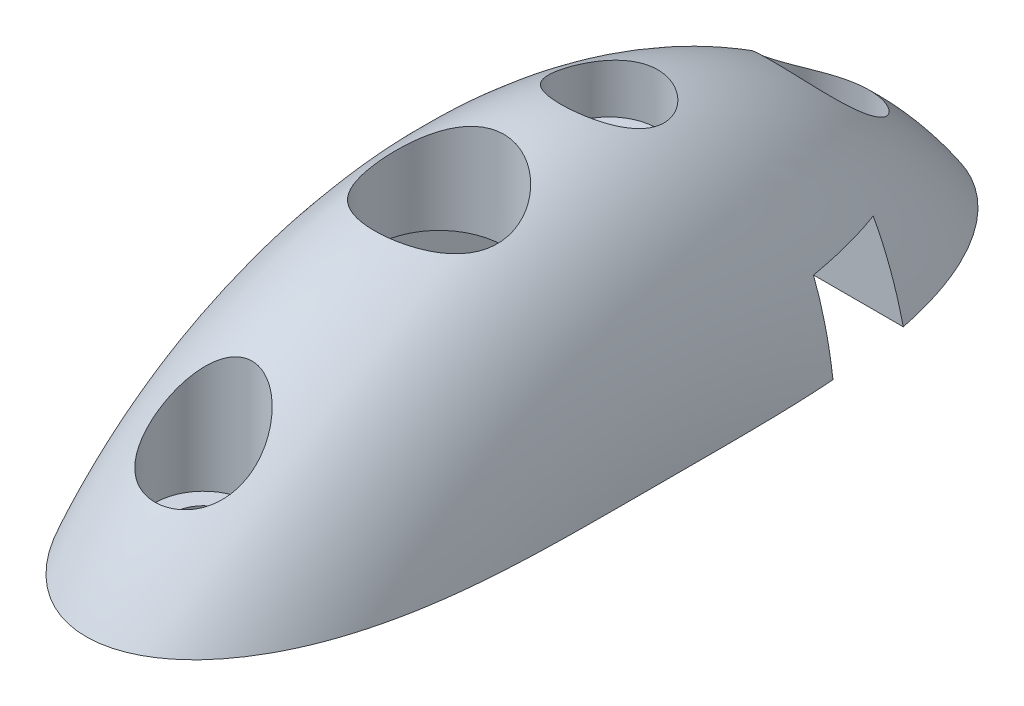
SolidWorks part; units mm, degrees
material "PET"
ref_plane "Front" through (0, 0, 0) normal (0, 0, 1) x (1, 0, 0)
ref_plane "Top" through (0, 0, 0) normal (0, 1, 0) x (1, 0, 0)
ref_plane "Right" through (0, 0, 0) normal (1, 0, 0) x (0, 0, -1)
sketch "Sketch1" plane through (0, 0, 0) normal (0, 0, 1) x (1, 0, 0)
  line L0 (0, 13.25) -> (0, 0) construction
  line L1 (-5.5, 8) -> (5.5, 8) construction
  line L2 (-5.5, 8) -> (-5.5, 0) construction
  line L3 (-5.5, 0) -> (5.5, 0) construction
  line L4 (5.5, 8) -> (5.5, 0) construction
  line L5 (-4, 8) -> (4, 8) construction
  line L6 (-4, 8) -> (-4, 13.25) construction
  line L7 (-4, 13.25) -> (4, 13.25) construction
  line L8 (4, 8) -> (4, 13.25) construction
  line L9 (-20.5845, -17.78) -> (20.5845, -17.78) construction
  line L10 (54.5, 8) -> (54.5, 13.25) construction
  line L11 (53.5, 0) -> (73.5, 0) construction
  line L12 (53.5, 0) -> (53.5, 8) construction
  line L13 (53.5, 8) -> (73.5, 8) construction
  line L14 (73.5, 0) -> (73.5, 8) construction
  line L15 (54.5, 13.25) -> (62.5, 13.25) construction
  line L16 (62.5, 13.25) -> (62.5, 8) construction
  line L17 (58.5, 13.25) -> (58.5, 0) construction
  line L18 (0, 13.97) -> (63.5, 13.97) construction
  line L19 (63.5, 13.97) -> (63.5, 0) construction
  line L20 (-9.525, 0) -> (-9.525, -17.78)
  line L21 (-9.525, -17.78) -> (9.525, -17.78)
  line L22 (9.525, -17.78) -> (9.525, 0)
  arc A1 (37.1954, 0) -> (89.8046, 0) centre (63.5, -17.78) cw construction
  ellipse E0 centre (0, 0) end of major axis (0, -13.97) minor radius 9.525 (9.525, 0) -> (-9.525, 0) ccw
  point P1 (0, 0)
  point P26 (1.8743, 17.9157)
  point P39 (0, 15.3735)
  point P40 (63.5, 14.7574)
  point P41 (34.4687, 0)
  dimension "D2" = 19.05
  dimension "D6" = 13.97
  dimension "D9" = 63.5
  dimension "D10" = 31.75
  dimension "D1" = 8
  dimension "D3" = 11
  dimension "D4" = 8
  dimension "D5" = 5.25
  dimension "D7" = 20
  dimension "D8" = 5
revolve "Revolve1" add sketch "Sketch1" angle 360 about L9
sketch "Sketch2" plane through (0, 0, 0) normal (0, 0, 1) x (1, 0, 0)
  line L1 (-9.525, 0) -> (9.525, 0)
  line L2 (-9.525, 0) -> (-9.525, -64.4391)
  line L3 (-9.525, -64.4391) -> (9.525, -64.4391)
  line L4 (9.525, 0) -> (9.525, -64.4391)
  line L5 (-9.525, 0) -> (-9.525, -35.56) construction
  point P10 (0, 0)
  point P11 (0, 0)
extrude "Cut-Extrude1" cut sketch "Sketch2" against normal through all both and the other way through all
sketch "Sketch3" plane through (0, 0, 0) normal (0, -1, 0) x (1, 0, 0)
  line L1 (6, -10.5) -> (-6, -10.5)
  line L2 (6, -10.5) -> (6, 10.5)
  line L3 (6, 10.5) -> (-6, 10.5)
  line L4 (-6, -10.5) -> (-6, 10.5)
  line L5 (6, -10.5) -> (-6, 10.5) construction
  line L6 (6, 10.5) -> (-6, -10.5) construction
  point P0 (0, 0)
  dimension "D1" = 21
  dimension "D2" = 12
extrude "Cut-Extrude2" cut sketch "Sketch3" against normal blind 8
sketch "Sketch4" plane through (0, 8, 0) normal (0, -1, 0) x (1, 0, 0)
  line L0 (-6, 10.5) -> (0, 4.5) construction
  line L1 (0, 4.5) -> (6, 10.5) construction
  circle A0 centre (0, 4.5) radius 4
  dimension "D1" = 8
extrude "Cut-Extrude3" cut sketch "Sketch4" against normal through all
sketch "Sketch5" plane through (0, 0, 0) normal (1, 0, 0) x (0, 0, -1)
  line L0 (-16.05, 13.97) -> (-16.05, 2.032)
  line L1 (-16.05, 2.032) -> (-17.145, 2.032)
  line L2 (-26.3046, 0) -> (26.3046, 0) construction
  line L3 (-17.145, 2.032) -> (-17.145, 0)
  line L5 (-17.145, 0) -> (-19.05, 0)
  line L6 (-19.05, 0) -> (-19.05, 13.97)
  line L7 (-19.05, 13.97) -> (-16.05, 13.97)
  line L8 (-19.05, 0) -> (-19.05, -2.083) construction
  point P2 (-19.05, 0)
  point P5 (0, 0)
  point P8 (0, 0)
  point P9 (-16.05, 13.504)
  point P13 (0, 0)
  dimension "D1" = 3.81
  dimension "D2" = 6
  dimension "D3" = 2.032
  dimension "D4" = 19.05
revolve "Cut-Revolve1" cut sketch "Sketch5" angle 360 about L8
mirror "Mirror1" about plane through (0, 0, 0) normal (0, 0, 1) of "Cut-Revolve1"
sketch "Sketch6" plane through (0, 0, 0) normal (1, 0, 0) x (0, 0, -1)
  line L0 (3, 13.97) -> (3, 9.524)
  line L1 (3, 9.524) -> (4.095, 9.524)
  line L2 (4.095, 9.524) -> (4.095, 0)
  line L3 (4.095, 0) -> (6, 0)
  line L4 (6, 0) -> (6, 13.97)
  line L5 (6, 13.97) -> (3, 13.97)
  line L6 (6, 0) -> (6, -2.8152) construction
  line L7 (-10.5, 8) -> (10.5, 8) construction
  line L9 (-4.5, 8) -> (-4.5, 3.6501) construction
  line L10 (-8.5, 8) -> (-0.5, 8) construction
  point P2 (3, 14.6614)
  dimension "D1" = 3.81
  dimension "D2" = 6
  dimension "D3" = 1.524
  dimension "D4" = 10.5
revolve "Cut-Revolve2" cut sketch "Sketch6" angle 360 about L6
sketch "Sketch7" plane through (0, 0, 0) normal (0, -1, 0) x (1, 0, 0)
  line L5 (-6, -10.5) -> (6, -10.5) construction
  line L6 (9.525, -10.5) -> (-9.525, -10.5)
  line L7 (9.525, -10.5) -> (9.525, -15.5)
  line L8 (9.525, -15.5) -> (-9.525, -15.5)
  line L9 (-9.525, -10.5) -> (-9.525, -15.5)
  point P4 (0, 0)
  point P5 (0, 0)
  point P6 (0, 0)
  point P7 (0, 0)
  dimension "D1" = 5
extrude "Cut-Extrude4" cut sketch "Sketch7" against normal blind 5
